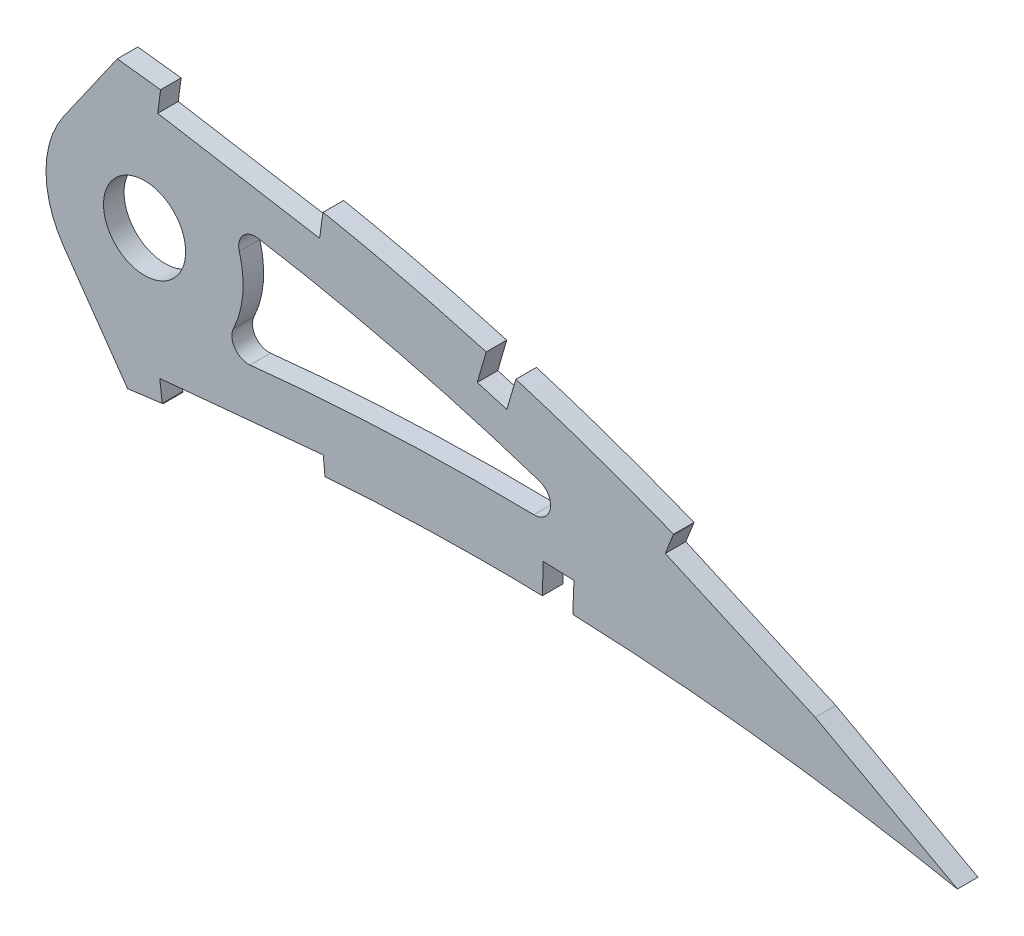
SolidWorks part; units mm, degrees
ref_plane "Front Plane" through (0, 0, 0) normal (0, 0, 1) x (1, 0, 0)
ref_plane "Top Plane" through (0, 0, 0) normal (0, 1, 0) x (1, 0, 0)
ref_plane "Right Plane" through (0, 0, 0) normal (1, 0, 0) x (0, 0, -1)
curve "Curve1"
  spline degree 3 poles (418.0125, 0.6517, 0) (417.9804, 0.6715, 0) (417.8525, 0.7505, 0) (417.5642, 0.9274, 0) (417.084, 1.2219, 0) (416.4119, 1.6322, 0) (415.5483, 2.157, 0) (414.4927, 2.7927, 0) (413.2459, 3.5372, 0) (411.8081, 4.387, 0) (410.1795, 5.3382, 0) (408.3608, 6.3869, 0) (406.352, 7.527, 0) (404.1539, 8.7541, 0) (401.7673, 10.0622, 0) (399.1927, 11.4455, 0) (396.4309, 12.8968, 0) (393.4831, 14.4101, 0) (390.3497, 15.9768, 0) (387.0323, 17.5905, 0) (383.532, 19.2431, 0) (379.8498, 20.9259, 0) (375.9881, 22.6319, 0) (371.9478, 24.3506, 0) (367.7312, 26.0745, 0) (363.3401, 27.7938, 0) (358.7771, 29.5006, 0) (354.0441, 31.184, 0) (349.1444, 32.8365, 0) (344.0806, 34.4474, 0) (338.8562, 36.008, 0) (333.4742, 37.5082, 0) (327.9392, 38.9402, 0) (322.2547, 40.2936, 0) (316.4254, 41.5594, 0) (310.456, 42.7299, 0) (304.3515, 43.7936, 0) (298.1289, 44.7494, 0) (291.8882, 45.5445, 0) (285.6603, 46.3243, 0) (279.4418, 47.0569, 0) (273.1472, 47.7584, 0) (266.7827, 48.425, 0) (260.3545, 49.0544, 0) (253.8692, 49.6441, 0) (247.3335, 50.1923, 0) (240.7538, 50.6959, 0) (234.1369, 51.1541, 0) (227.4895, 51.5628, 0) (220.8185, 51.9218, 0) (214.1308, 52.2286, 0) (207.4334, 52.481, 0) (200.7332, 52.6776, 0) (194.0374, 52.8164, 0) (187.3531, 52.8966, 0) (180.6873, 52.916, 0) (174.0473, 52.8742, 0) (167.44, 52.7698, 0) (160.8726, 52.6014, 0) (154.3521, 52.3686, 0) (147.8856, 52.0716, 0) (141.4801, 51.7078, 0) (135.1426, 51.2797, 0) (128.8802, 50.7853, 0) (122.6997, 50.2246, 0) (116.6076, 49.5999, 0) (110.6107, 48.9095, 0) (104.7154, 48.1553, 0) (98.9282, 47.3389, 0) (93.2555, 46.4598, 0) (87.7035, 45.5205, 0) (82.2781, 44.522, 0) (76.9851, 43.4673, 0) (71.8302, 42.3565, 0) (66.8189, 41.1931, 0) (61.9564, 39.979, 0) (57.2479, 38.7165, 0) (52.6982, 37.4086, 0) (48.3119, 36.0583, 0) (44.0941, 34.667, 0) (40.048, 33.2401, 0) (36.1786, 31.7785, 0) (32.4888, 30.2868, 0) (28.983, 28.767, 0) (25.6637, 27.2237, 0) (22.5348, 25.6586, 0) (19.5984, 24.0762, 0) (16.8576, 22.4789, 0) (14.3149, 20.8697, 0) (11.9714, 19.2526, 0) (9.8303, 17.6287, 0) (7.8925, 16.002, 0) (6.159, 14.375, 0) (4.6325, 12.7489, 0) (3.3127, 11.1265, 0) (2.2016, 9.5091, 0) (1.2991, 7.8983, 0) (0.6075, 6.2951, 0) (0.126, 4.7006, 0) (-0.1376, 3.117, 0) (-0.2032, 1.5431, 0) (-0.0676, 0.5136, 0) (0, 0, 0) knots 0 0 0 0 0.000254 0.001015 0.002283 0.004057 0.006331 0.009105 0.012374 0.016134 0.02038 0.025106 0.030306 0.035972 0.0421 0.048678 0.055702 0.06316 0.071046 0.07935 0.088063 0.097176 0.106678 0.116562 0.126814 0.137428 0.148394 0.1597 0.171338 0.183298 0.19557 0.208144 0.221012 0.234162 0.247587 0.261277 0.275223 0.289414 0.303771 0.317689 0.331784 0.34604 0.360444 0.374983 0.38964 0.404403 0.419257 0.434187 0.449177 0.464215 0.479284 0.49437 0.509458 0.524532 0.539579 0.554583 0.56953 0.584403 0.599191 0.613877 0.628447 0.642889 0.657186 0.671326 0.685294 0.699078 0.712665 0.726043 0.739198 0.752118 0.764792 0.777208 0.789356 0.801224 0.812804 0.824083 0.835055 0.84571 0.856038 0.866034 0.875689 0.884998 0.893953 0.902553 0.910789 0.918661 0.926166 0.933303 0.940071 0.946475 0.952518 0.958205 0.963547 0.968557 0.97325 0.977651 0.981787 0.985694 0.989415 0.993001 0.996508 1 1 1 1
curve "Curve2"
  spline degree 3 poles (0, 0, 0) (0.1073, -0.5067, 0) (0.3225, -1.5225, 0) (0.9071, -2.9849, 0) (1.6803, -4.3906, 0) (2.6581, -5.736, 0) (3.8343, -7.0207, 0) (5.206, -8.246, 0) (6.772, -9.4112, 0) (8.5303, -10.5159, 0) (10.4783, -11.5612, 0) (12.6138, -12.5465, 0) (14.9348, -13.4715, 0) (17.4389, -14.3348, 0) (20.1229, -15.1379, 0) (22.9843, -15.8787, 0) (26.0199, -16.5584, 0) (29.2267, -17.1751, 0) (32.6013, -17.7296, 0) (36.1401, -18.2214, 0) (39.8395, -18.651, 0) (43.6959, -19.0173, 0) (47.7054, -19.3212, 0) (51.8641, -19.5629, 0) (56.168, -19.7432, 0) (60.6128, -19.8613, 0) (65.1943, -19.9191, 0) (69.9083, -19.9175, 0) (74.7502, -19.8561, 0) (79.7159, -19.7382, 0) (84.8006, -19.5631, 0) (89.9997, -19.3329, 0) (95.3085, -19.05, 0) (100.7222, -18.7153, 0) (106.2362, -18.3302, 0) (111.8455, -17.8979, 0) (117.5452, -17.4195, 0) (123.3302, -16.8976, 0) (129.1955, -16.3351, 0) (135.1358, -15.7335, 0) (141.1461, -15.0958, 0) (147.221, -14.4241, 0) (153.3552, -13.7218, 0) (159.5432, -12.9903, 0) (165.7798, -12.2338, 0) (172.059, -11.4536, 0) (178.3757, -10.6529, 0) (184.7241, -9.8353, 0) (191.0984, -9.0009, 0) (197.493, -8.1554, 0) (203.902, -7.2983, 0) (210.3197, -6.4339, 0) (216.7401, -5.5649, 0) (223.157, -4.6917, 0) (229.5648, -3.8177, 0) (235.9575, -2.9455, 0) (242.3289, -2.075, 0) (248.6732, -1.2107, 0) (254.984, -0.3523, 0) (261.2554, 0.4983, 0) (267.4816, 1.3385, 0) (273.6565, 2.1675, 0) (279.7739, 2.9846, 0) (285.8276, 3.7901, 0) (291.7208, 4.5595, 0) (297.4382, 5.334, 0) (302.999, 5.9689, 0) (308.4906, 6.5107, 0) (313.9186, 6.955, 0) (319.2766, 7.3081, 0) (324.5584, 7.5724, 0) (329.7577, 7.7517, 0) (334.868, 7.8514, 0) (339.8828, 7.8739, 0) (344.7953, 7.8264, 0) (349.5992, 7.7127, 0) (354.2877, 7.538, 0) (358.8543, 7.3082, 0) (363.2925, 7.0294, 0) (367.5956, 6.7058, 0) (371.7576, 6.345, 0) (375.7722, 5.9523, 0) (379.6331, 5.5321, 0) (383.3347, 5.0933, 0) (386.8711, 4.6386, 0) (390.237, 4.1757, 0) (393.427, 3.7092, 0) (396.4359, 3.245, 0) (399.2592, 2.7876, 0) (401.8921, 2.3431, 0) (404.3306, 1.9155, 0) (406.5705, 1.5092, 0) (408.6087, 1.1291, 0) (410.4411, 0.7773, 0) (412.0652, 0.4594, 0) (413.4782, 0.1769, 0) (414.6777, -0.0662, 0) (415.6619, -0.269, 0) (416.4292, -0.4281, 0) (416.9781, -0.5438, 0) (417.3079, -0.6126, 0) (417.4545, -0.6439, 0) (417.4911, -0.6517, 0) knots 0 0 0 0 0.003638 0.007293 0.011028 0.014901 0.018963 0.023258 0.027821 0.032679 0.037853 0.043362 0.049215 0.055422 0.061989 0.068918 0.076211 0.083868 0.091887 0.100266 0.109 0.118085 0.127515 0.137285 0.147388 0.157816 0.168563 0.179619 0.190977 0.202627 0.21456 0.226767 0.239236 0.251959 0.264924 0.27812 0.291536 0.30516 0.318981 0.332985 0.347163 0.361499 0.375981 0.390597 0.405333 0.420175 0.43511 0.450124 0.465203 0.480333 0.495501 0.51069 0.525887 0.541078 0.556247 0.571382 0.586466 0.601485 0.616424 0.631269 0.646007 0.660621 0.675098 0.689423 0.703582 0.716908 0.730009 0.742952 0.755726 0.76832 0.780724 0.792927 0.804916 0.816679 0.828204 0.839475 0.850481 0.861208 0.871639 0.881763 0.891564 0.901027 0.910139 0.918884 0.927249 0.935221 0.942785 0.949928 0.956638 0.962904 0.968712 0.974054 0.978918 0.983297 0.98718 0.990561 0.993433 0.995791 0.99763 0.998946 0.999737 1 1 1 1
sketch "Sketch1" plane through (0, 0, 0) normal (0, 0, 1) x (1, 0, 0)
  line L25 (417.4911, -0.6517) -> (421.451, -1.4725)
  line L26 (418.0125, 0.6517) -> (421.451, -1.4725)
  spline S2 degree 3 poles (-2901.6072, -758.8258) (62.2286, 60.9377) (-7.5382, 18.1399) (0.9071, -2.9849) (1.6803, -4.3906) (2.6581, -5.736) (3.8343, -7.0207) (5.206, -8.246) (6.772, -9.4112) (8.5303, -10.5159) (10.4783, -11.5612) (12.6138, -12.5465) (14.9348, -13.4715) (17.4389, -14.3348) (20.1229, -15.1379) (22.9843, -15.8787) (26.0199, -16.5584) (29.2267, -17.1751) (32.6013, -17.7296) (36.1401, -18.2214) (39.8395, -18.651) (43.6959, -19.0173) (47.7054, -19.3212) (51.8641, -19.5629) (56.168, -19.7432) (60.6128, -19.8613) (65.1943, -19.9191) (69.9083, -19.9175) (74.7502, -19.8561) (79.7159, -19.7382) (84.8006, -19.5631) (89.9997, -19.3329) (95.3085, -19.05) (100.7222, -18.7153) (106.2362, -18.3302) (111.8455, -17.8979) (117.5452, -17.4195) (123.3302, -16.8976) (129.1955, -16.3351) (135.1358, -15.7335) (141.1461, -15.0958) (147.221, -14.4241) (153.3552, -13.7218) (159.5432, -12.9903) (165.7798, -12.2338) (172.059, -11.4536) (178.3757, -10.6529) (184.7241, -9.8353) (191.0984, -9.0009) (197.493, -8.1554) (203.902, -7.2983) (210.3197, -6.4339) (216.7401, -5.5649) (223.157, -4.6917) (229.5648, -3.8177) (235.9575, -2.9455) (242.3289, -2.075) (248.6732, -1.2107) (254.984, -0.3523) (261.2554, 0.4983) (267.4816, 1.3385) (273.6565, 2.1675) (279.7739, 2.9846) (285.8276, 3.7901) (291.7208, 4.5595) (297.4382, 5.334) (302.999, 5.9689) (308.4906, 6.5107) (313.9186, 6.955) (319.2766, 7.3081) (324.5584, 7.5724) (329.7577, 7.7517) (334.868, 7.8514) (339.8828, 7.8739) (344.7953, 7.8264) (349.5992, 7.7127) (354.2877, 7.538) (358.8543, 7.3082) (363.2925, 7.0294) (367.5956, 6.7058) (371.7576, 6.345) (375.7722, 5.9523) (379.6331, 5.5321) (383.3347, 5.0933) (386.8711, 4.6386) (390.237, 4.1757) (393.427, 3.7092) (396.4359, 3.245) (399.2592, 2.7876) (401.8921, 2.3431) (404.3306, 1.9155) (406.5705, 1.5092) (408.6087, 1.1291) (410.4411, 0.7773) (412.0652, 0.4594) (413.4782, 0.1769) (414.6777, -0.0662) (415.6619, -0.269) (416.4292, -0.4281) (416.9781, -0.5438) (432.6216, -3.8089) (446.5682, -14.1933) (1083.8628, 2923.4074) knots -0.148283 -0.148283 -0.148283 -0.148283 0.003638 0.007293 0.011028 0.014901 0.018963 0.023258 0.027821 0.032679 0.037853 0.043362 0.049215 0.055422 0.061989 0.068918 0.076211 0.083868 0.091887 0.100266 0.109 0.118085 0.127515 0.137285 0.147388 0.157816 0.168563 0.179619 0.190977 0.202627 0.21456 0.226767 0.239236 0.251959 0.264924 0.27812 0.291536 0.30516 0.318981 0.332985 0.347163 0.361499 0.375981 0.390597 0.405333 0.420175 0.43511 0.450124 0.465203 0.480333 0.495501 0.51069 0.525887 0.541078 0.556247 0.571382 0.586466 0.601485 0.616424 0.631269 0.646007 0.660621 0.675098 0.689423 0.703582 0.716908 0.730009 0.742952 0.755726 0.76832 0.780724 0.792927 0.804916 0.816679 0.828204 0.839475 0.850481 0.861208 0.871639 0.881763 0.891564 0.901027 0.910139 0.918884 0.927249 0.935221 0.942785 0.949928 0.956638 0.962904 0.968712 0.974054 0.978918 0.983297 0.98718 0.990561 0.993433 0.995791 0.99763 0.998946 0.999737 1.110049 1.110049 1.110049 1.110049 only from (0, 0) to (417.4911, -0.6517) construction
  spline S3 degree 3 poles (2035.6651, 2526.3996) (444.3669, -23.2124) (432.7668, -8.3977) (417.5642, 0.9274) (417.084, 1.2219) (416.4119, 1.6322) (415.5483, 2.157) (414.4927, 2.7927) (413.2459, 3.5372) (411.8081, 4.387) (410.1795, 5.3382) (408.3608, 6.3869) (406.352, 7.527) (404.1539, 8.7541) (401.7673, 10.0622) (399.1927, 11.4455) (396.4309, 12.8968) (393.4831, 14.4101) (390.3497, 15.9768) (387.0323, 17.5905) (383.532, 19.2431) (379.8498, 20.9259) (375.9881, 22.6319) (371.9478, 24.3506) (367.7312, 26.0745) (363.3401, 27.7938) (358.7771, 29.5006) (354.0441, 31.184) (349.1444, 32.8365) (344.0806, 34.4474) (338.8562, 36.008) (333.4742, 37.5082) (327.9392, 38.9402) (322.2547, 40.2936) (316.4254, 41.5594) (310.456, 42.7299) (304.3515, 43.7936) (298.1289, 44.7494) (291.8882, 45.5445) (285.6603, 46.3243) (279.4418, 47.0569) (273.1472, 47.7584) (266.7827, 48.425) (260.3545, 49.0544) (253.8692, 49.6441) (247.3335, 50.1923) (240.7538, 50.6959) (234.1369, 51.1541) (227.4895, 51.5628) (220.8185, 51.9218) (214.1308, 52.2286) (207.4334, 52.481) (200.7332, 52.6776) (194.0374, 52.8164) (187.3531, 52.8966) (180.6873, 52.916) (174.0473, 52.8742) (167.44, 52.7698) (160.8726, 52.6014) (154.3521, 52.3686) (147.8856, 52.0716) (141.4801, 51.7078) (135.1426, 51.2797) (128.8802, 50.7853) (122.6997, 50.2246) (116.6076, 49.5999) (110.6107, 48.9095) (104.7154, 48.1553) (98.9282, 47.3389) (93.2555, 46.4598) (87.7035, 45.5205) (82.2781, 44.522) (76.9851, 43.4673) (71.8302, 42.3565) (66.8189, 41.1931) (61.9564, 39.979) (57.2479, 38.7165) (52.6982, 37.4086) (48.3119, 36.0583) (44.0941, 34.667) (40.048, 33.2401) (36.1786, 31.7785) (32.4888, 30.2868) (28.983, 28.767) (25.6637, 27.2237) (22.5348, 25.6586) (19.5984, 24.0762) (16.8576, 22.4789) (14.3149, 20.8697) (11.9714, 19.2526) (9.8303, 17.6287) (7.8925, 16.002) (6.159, 14.375) (4.6325, 12.7489) (3.3127, 11.1265) (2.2016, 9.5091) (1.2991, 7.8983) (0.6075, 6.2951) (0.126, 4.7006) (-0.1376, 3.117) (-1.0834, -19.5745) (79.1081, -36.6721) (-2988.5065, -249.641) knots -0.11811 -0.11811 -0.11811 -0.11811 0.000254 0.001015 0.002283 0.004057 0.006331 0.009105 0.012374 0.016134 0.02038 0.025106 0.030306 0.035972 0.0421 0.048678 0.055702 0.06316 0.071046 0.07935 0.088063 0.097176 0.106678 0.116562 0.126814 0.137428 0.148394 0.1597 0.171338 0.183298 0.19557 0.208144 0.221012 0.234162 0.247587 0.261277 0.275223 0.289414 0.303771 0.317689 0.331784 0.34604 0.360444 0.374983 0.38964 0.404403 0.419257 0.434187 0.449177 0.464215 0.479284 0.49437 0.509458 0.524532 0.539579 0.554583 0.56953 0.584403 0.599191 0.613877 0.628447 0.642889 0.657186 0.671326 0.685294 0.699078 0.712665 0.726043 0.739198 0.752118 0.764792 0.777208 0.789356 0.801224 0.812804 0.824083 0.835055 0.84571 0.856038 0.866034 0.875689 0.884998 0.893953 0.902553 0.910789 0.918661 0.926166 0.933303 0.940071 0.946475 0.952518 0.958205 0.963547 0.968557 0.97325 0.977651 0.981787 0.985694 0.989415 0.993001 0.996508 1.142022 1.142022 1.142022 1.142022 only from (418.0125, 0.6517) to (0, 0) construction
  spline S4 degree 3 poles (0, 0) (0.1073, -0.5067) (0.3225, -1.5225) (0.9071, -2.9849) (1.6803, -4.3906) (2.6581, -5.736) (3.8343, -7.0207) (5.206, -8.246) (6.772, -9.4112) (8.5303, -10.5159) (10.4783, -11.5612) (12.6138, -12.5465) (14.9348, -13.4715) (17.4389, -14.3348) (20.1229, -15.1379) (22.9843, -15.8787) (26.0199, -16.5584) (29.2267, -17.1751) (32.6013, -17.7296) (36.1401, -18.2214) (39.8395, -18.651) (43.6959, -19.0173) (47.7054, -19.3212) (51.8641, -19.5629) (56.168, -19.7432) (60.6128, -19.8613) (65.1943, -19.9191) (69.9083, -19.9175) (74.7502, -19.8561) (79.7159, -19.7382) (84.8006, -19.5631) (89.9997, -19.3329) (95.3085, -19.05) (100.7222, -18.7153) (106.2362, -18.3302) (111.8455, -17.8979) (117.5452, -17.4195) (123.3302, -16.8976) (129.1955, -16.3351) (135.1358, -15.7335) (141.1461, -15.0958) (147.221, -14.4241) (153.3552, -13.7218) (159.5432, -12.9903) (165.7798, -12.2338) (172.059, -11.4536) (178.3757, -10.6529) (184.7241, -9.8353) (191.0984, -9.0009) (197.493, -8.1554) (203.902, -7.2983) (210.3197, -6.4339) (216.7401, -5.5649) (223.157, -4.6917) (229.5648, -3.8177) (235.9575, -2.9455) (242.3289, -2.075) (248.6732, -1.2107) (254.984, -0.3523) (261.2554, 0.4983) (267.4816, 1.3385) (273.6565, 2.1675) (279.7739, 2.9846) (285.8276, 3.7901) (291.7208, 4.5595) (297.4382, 5.334) (302.999, 5.9689) (308.4906, 6.5107) (313.9186, 6.955) (319.2766, 7.3081) (324.5584, 7.5724) (329.7577, 7.7517) (334.868, 7.8514) (339.8828, 7.8739) (344.7953, 7.8264) (349.5992, 7.7127) (354.2877, 7.538) (358.8543, 7.3082) (363.2925, 7.0294) (367.5956, 6.7058) (371.7576, 6.345) (375.7722, 5.9523) (379.6331, 5.5321) (383.3347, 5.0933) (386.8711, 4.6386) (390.237, 4.1757) (393.427, 3.7092) (396.4359, 3.245) (399.2592, 2.7876) (401.8921, 2.3431) (404.3306, 1.9155) (406.5705, 1.5092) (408.6087, 1.1291) (410.4411, 0.7773) (412.0652, 0.4594) (413.4782, 0.1769) (414.6777, -0.0662) (415.6619, -0.269) (416.4292, -0.4281) (416.9781, -0.5438) (417.3079, -0.6126) (417.4545, -0.6439) (417.4911, -0.6517) knots 0 0 0 0 0.003638 0.007293 0.011028 0.014901 0.018963 0.023258 0.027821 0.032679 0.037853 0.043362 0.049215 0.055422 0.061989 0.068918 0.076211 0.083868 0.091887 0.100266 0.109 0.118085 0.127515 0.137285 0.147388 0.157816 0.168563 0.179619 0.190977 0.202627 0.21456 0.226767 0.239236 0.251959 0.264924 0.27812 0.291536 0.30516 0.318981 0.332985 0.347163 0.361499 0.375981 0.390597 0.405333 0.420175 0.43511 0.450124 0.465203 0.480333 0.495501 0.51069 0.525887 0.541078 0.556247 0.571382 0.586466 0.601485 0.616424 0.631269 0.646007 0.660621 0.675098 0.689423 0.703582 0.716908 0.730009 0.742952 0.755726 0.76832 0.780724 0.792927 0.804916 0.816679 0.828204 0.839475 0.850481 0.861208 0.871639 0.881763 0.891564 0.901027 0.910139 0.918884 0.927249 0.935221 0.942785 0.949928 0.956638 0.962904 0.968712 0.974054 0.978918 0.983297 0.98718 0.990561 0.993433 0.995791 0.99763 0.998946 0.999737 1 1 1 1
  spline S5 degree 3 poles (418.0125, 0.6517) (417.9804, 0.6715) (417.8525, 0.7505) (417.5642, 0.9274) (417.084, 1.2219) (416.4119, 1.6322) (415.5483, 2.157) (414.4927, 2.7927) (413.2459, 3.5372) (411.8081, 4.387) (410.1795, 5.3382) (408.3608, 6.3869) (406.352, 7.527) (404.1539, 8.7541) (401.7673, 10.0622) (399.1927, 11.4455) (396.4309, 12.8968) (393.4831, 14.4101) (390.3497, 15.9768) (387.0323, 17.5905) (383.532, 19.2431) (379.8498, 20.9259) (375.9881, 22.6319) (371.9478, 24.3506) (367.7312, 26.0745) (363.3401, 27.7938) (358.7771, 29.5006) (354.0441, 31.184) (349.1444, 32.8365) (344.0806, 34.4474) (338.8562, 36.008) (333.4742, 37.5082) (327.9392, 38.9402) (322.2547, 40.2936) (316.4254, 41.5594) (310.456, 42.7299) (304.3515, 43.7936) (298.1289, 44.7494) (291.8882, 45.5445) (285.6603, 46.3243) (279.4418, 47.0569) (273.1472, 47.7584) (266.7827, 48.425) (260.3545, 49.0544) (253.8692, 49.6441) (247.3335, 50.1923) (240.7538, 50.6959) (234.1369, 51.1541) (227.4895, 51.5628) (220.8185, 51.9218) (214.1308, 52.2286) (207.4334, 52.481) (200.7332, 52.6776) (194.0374, 52.8164) (187.3531, 52.8966) (180.6873, 52.916) (174.0473, 52.8742) (167.44, 52.7698) (160.8726, 52.6014) (154.3521, 52.3686) (147.8856, 52.0716) (141.4801, 51.7078) (135.1426, 51.2797) (128.8802, 50.7853) (122.6997, 50.2246) (116.6076, 49.5999) (110.6107, 48.9095) (104.7154, 48.1553) (98.9282, 47.3389) (93.2555, 46.4598) (87.7035, 45.5205) (82.2781, 44.522) (76.9851, 43.4673) (71.8302, 42.3565) (66.8189, 41.1931) (61.9564, 39.979) (57.2479, 38.7165) (52.6982, 37.4086) (48.3119, 36.0583) (44.0941, 34.667) (40.048, 33.2401) (36.1786, 31.7785) (32.4888, 30.2868) (28.983, 28.767) (25.6637, 27.2237) (22.5348, 25.6586) (19.5984, 24.0762) (16.8576, 22.4789) (14.3149, 20.8697) (11.9714, 19.2526) (9.8303, 17.6287) (7.8925, 16.002) (6.159, 14.375) (4.6325, 12.7489) (3.3127, 11.1265) (2.2016, 9.5091) (1.2991, 7.8983) (0.6075, 6.2951) (0.126, 4.7006) (-0.1376, 3.117) (-0.2032, 1.5431) (-0.0676, 0.5136) (0, 0) knots 0 0 0 0 0.000254 0.001015 0.002283 0.004057 0.006331 0.009105 0.012374 0.016134 0.02038 0.025106 0.030306 0.035972 0.0421 0.048678 0.055702 0.06316 0.071046 0.07935 0.088063 0.097176 0.106678 0.116562 0.126814 0.137428 0.148394 0.1597 0.171338 0.183298 0.19557 0.208144 0.221012 0.234162 0.247587 0.261277 0.275223 0.289414 0.303771 0.317689 0.331784 0.34604 0.360444 0.374983 0.38964 0.404403 0.419257 0.434187 0.449177 0.464215 0.479284 0.49437 0.509458 0.524532 0.539579 0.554583 0.56953 0.584403 0.599191 0.613877 0.628447 0.642889 0.657186 0.671326 0.685294 0.699078 0.712665 0.726043 0.739198 0.752118 0.764792 0.777208 0.789356 0.801224 0.812804 0.824083 0.835055 0.84571 0.856038 0.866034 0.875689 0.884998 0.893953 0.902553 0.910789 0.918661 0.926166 0.933303 0.940071 0.946475 0.952518 0.958205 0.963547 0.968557 0.97325 0.977651 0.981787 0.985694 0.989415 0.993001 0.996508 1 1 1 1
extrude "Boss-Extrude1" add sketch "Sketch1" along normal blind 3.175
sketch "Sketch3" plane through (0, 0, 0) normal (0, 0, -1) x (-1, 0, 0)
  circle A1 centre (-285.7292, 26.2554) radius 6.35
extrude "Cut-Extrude2" cut sketch "Sketch3" against normal blind 7.62
sketch "Sketch4" plane through (0, 0, 3.175) normal (0, 0, 1) x (1, 0, 0)
  line L0 (273.2453, 34.9967) -> (281.5171, 46.8101)
  line L1 (273.2453, 17.5141) -> (283.1086, 3.4278)
  line L2 (285.7292, 26.2554) -> (311.044, 26.2554)
  circle A0 centre (285.7292, 26.2554) radius 6.35 construction
  circle A1 centre (285.7292, 26.2554) radius 6.35
  circle A2 centre (285.7292, 26.2554) radius 15.24
  spline S0 degree 3 poles (-1937.7253, -493.2296) (46.5589, 50.9528) (-6.5452, 15.6559) (0.9071, -2.9849) (1.6803, -4.3906) (2.6581, -5.736) (3.8343, -7.0207) (5.206, -8.246) (6.772, -9.4112) (8.5303, -10.5159) (10.4783, -11.5612) (12.6138, -12.5465) (14.9348, -13.4715) (17.4389, -14.3348) (20.1229, -15.1379) (22.9843, -15.8787) (26.0199, -16.5584) (29.2267, -17.1751) (32.6013, -17.7296) (36.1401, -18.2214) (39.8395, -18.651) (43.6959, -19.0173) (47.7054, -19.3212) (51.8641, -19.5629) (56.168, -19.7432) (60.6128, -19.8613) (65.1943, -19.9191) (69.9083, -19.9175) (74.7502, -19.8561) (79.7159, -19.7382) (84.8006, -19.5631) (89.9997, -19.3329) (95.3085, -19.05) (100.7222, -18.7153) (106.2362, -18.3302) (111.8455, -17.8979) (117.5452, -17.4195) (123.3302, -16.8976) (129.1955, -16.3351) (135.1358, -15.7335) (141.1461, -15.0958) (147.221, -14.4241) (153.3552, -13.7218) (159.5432, -12.9903) (165.7798, -12.2338) (172.059, -11.4536) (178.3757, -10.6529) (184.7241, -9.8353) (191.0984, -9.0009) (197.493, -8.1554) (203.902, -7.2983) (210.3197, -6.4339) (216.7401, -5.5649) (223.157, -4.6917) (229.5648, -3.8177) (235.9575, -2.9455) (242.3289, -2.075) (248.6732, -1.2107) (254.984, -0.3523) (261.2554, 0.4983) (267.4816, 1.3385) (273.6565, 2.1675) (279.7739, 2.9846) (285.8276, 3.7901) (291.7208, 4.5595) (297.4382, 5.334) (302.999, 5.9689) (308.4906, 6.5107) (313.9186, 6.955) (319.2766, 7.3081) (324.5584, 7.5724) (329.7577, 7.7517) (334.868, 7.8514) (339.8828, 7.8739) (344.7953, 7.8264) (349.5992, 7.7127) (354.2877, 7.538) (358.8543, 7.3082) (363.2925, 7.0294) (367.5956, 6.7058) (371.7576, 6.345) (375.7722, 5.9523) (379.6331, 5.5321) (383.3347, 5.0933) (386.8711, 4.6386) (390.237, 4.1757) (393.427, 3.7092) (396.4359, 3.245) (399.2592, 2.7876) (401.8921, 2.3431) (404.3306, 1.9155) (406.5705, 1.5092) (408.6087, 1.1291) (410.4411, 0.7773) (412.0652, 0.4594) (413.4782, 0.1769) (414.6777, -0.0662) (415.6619, -0.269) (416.4292, -0.4281) (416.9781, -0.5438) (430.6853, -3.4047) (443.0511, -11.7044) (871.2046, 1946.5522) knots -0.129551 -0.129551 -0.129551 -0.129551 0.003638 0.007293 0.011028 0.014901 0.018963 0.023258 0.027821 0.032679 0.037853 0.043362 0.049215 0.055422 0.061989 0.068918 0.076211 0.083868 0.091887 0.100266 0.109 0.118085 0.127515 0.137285 0.147388 0.157816 0.168563 0.179619 0.190977 0.202627 0.21456 0.226767 0.239236 0.251959 0.264924 0.27812 0.291536 0.30516 0.318981 0.332985 0.347163 0.361499 0.375981 0.390597 0.405333 0.420175 0.43511 0.450124 0.465203 0.480333 0.495501 0.51069 0.525887 0.541078 0.556247 0.571382 0.586466 0.601485 0.616424 0.631269 0.646007 0.660621 0.675098 0.689423 0.703582 0.716908 0.730009 0.742952 0.755726 0.76832 0.780724 0.792927 0.804916 0.816679 0.828204 0.839475 0.850481 0.861208 0.871639 0.881763 0.891564 0.901027 0.910139 0.918884 0.927249 0.935221 0.942785 0.949928 0.956638 0.962904 0.968712 0.974054 0.978918 0.983297 0.98718 0.990561 0.993433 0.995791 0.99763 0.998946 0.999737 1.096134 1.096134 1.096134 1.096134 only from (0, 0) to (417.4911, -0.6517) construction
  spline S1 degree 3 poles (1505.5404, 1678.541) (441.4039, -19.5852) (430.8807, -7.2408) (417.5642, 0.9274) (417.084, 1.2219) (416.4119, 1.6322) (415.5483, 2.157) (414.4927, 2.7927) (413.2459, 3.5372) (411.8081, 4.387) (410.1795, 5.3382) (408.3608, 6.3869) (406.352, 7.527) (404.1539, 8.7541) (401.7673, 10.0622) (399.1927, 11.4455) (396.4309, 12.8968) (393.4831, 14.4101) (390.3497, 15.9768) (387.0323, 17.5905) (383.532, 19.2431) (379.8498, 20.9259) (375.9881, 22.6319) (371.9478, 24.3506) (367.7312, 26.0745) (363.3401, 27.7938) (358.7771, 29.5006) (354.0441, 31.184) (349.1444, 32.8365) (344.0806, 34.4474) (338.8562, 36.008) (333.4742, 37.5082) (327.9392, 38.9402) (322.2547, 40.2936) (316.4254, 41.5594) (310.456, 42.7299) (304.3515, 43.7936) (298.1289, 44.7494) (291.8882, 45.5445) (285.6603, 46.3243) (279.4418, 47.0569) (273.1472, 47.7584) (266.7827, 48.425) (260.3545, 49.0544) (253.8692, 49.6441) (247.3335, 50.1923) (240.7538, 50.6959) (234.1369, 51.1541) (227.4895, 51.5628) (220.8185, 51.9218) (214.1308, 52.2286) (207.4334, 52.481) (200.7332, 52.6776) (194.0374, 52.8164) (187.3531, 52.8966) (180.6873, 52.916) (174.0473, 52.8742) (167.44, 52.7698) (160.8726, 52.6014) (154.3521, 52.3686) (147.8856, 52.0716) (141.4801, 51.7078) (135.1426, 51.2797) (128.8802, 50.7853) (122.6997, 50.2246) (116.6076, 49.5999) (110.6107, 48.9095) (104.7154, 48.1553) (98.9282, 47.3389) (93.2555, 46.4598) (87.7035, 45.5205) (82.2781, 44.522) (76.9851, 43.4673) (71.8302, 42.3565) (66.8189, 41.1931) (61.9564, 39.979) (57.2479, 38.7165) (52.6982, 37.4086) (48.3119, 36.0583) (44.0941, 34.667) (40.048, 33.2401) (36.1786, 31.7785) (32.4888, 30.2868) (28.983, 28.767) (25.6637, 27.2237) (22.5348, 25.6586) (19.5984, 24.0762) (16.8576, 22.4789) (14.3149, 20.8697) (11.9714, 19.2526) (9.8303, 17.6287) (7.8925, 16.002) (6.159, 14.375) (4.6325, 12.7489) (3.3127, 11.1265) (2.2016, 9.5091) (1.2991, 7.8983) (0.6075, 6.2951) (0.126, 4.7006) (-0.1376, 3.117) (-0.9722, -16.9072) (60.9773, -32.4825) (-1991.3982, -179.4503) knots -0.103174 -0.103174 -0.103174 -0.103174 0.000254 0.001015 0.002283 0.004057 0.006331 0.009105 0.012374 0.016134 0.02038 0.025106 0.030306 0.035972 0.0421 0.048678 0.055702 0.06316 0.071046 0.07935 0.088063 0.097176 0.106678 0.116562 0.126814 0.137428 0.148394 0.1597 0.171338 0.183298 0.19557 0.208144 0.221012 0.234162 0.247587 0.261277 0.275223 0.289414 0.303771 0.317689 0.331784 0.34604 0.360444 0.374983 0.38964 0.404403 0.419257 0.434187 0.449177 0.464215 0.479284 0.49437 0.509458 0.524532 0.539579 0.554583 0.56953 0.584403 0.599191 0.613877 0.628447 0.642889 0.657186 0.671326 0.685294 0.699078 0.712665 0.726043 0.739198 0.752118 0.764792 0.777208 0.789356 0.801224 0.812804 0.824083 0.835055 0.84571 0.856038 0.866034 0.875689 0.884998 0.893953 0.902553 0.910789 0.918661 0.926166 0.933303 0.940071 0.946475 0.952518 0.958205 0.963547 0.968557 0.97325 0.977651 0.981787 0.985694 0.989415 0.993001 0.996508 1.124083 1.124083 1.124083 1.124083 only from (418.0125, 0.6517) to (0, 0) construction
  spline S2 degree 3 poles (180.4181, -10.3891) (181.8505, -10.2052) (185.4085, -9.7457) (191.0984, -9.0009) (197.493, -8.1554) (203.902, -7.2983) (210.3197, -6.4339) (216.7401, -5.5649) (223.157, -4.6917) (229.5648, -3.8177) (235.9575, -2.9455) (242.3289, -2.075) (248.6732, -1.2107) (254.984, -0.3523) (261.2554, 0.4983) (267.4816, 1.3385) (273.6565, 2.1675) (279.7739, 2.9846) (285.8276, 3.7901) (291.7208, 4.5595) (297.4382, 5.334) (302.999, 5.9689) (308.4906, 6.5107) (313.9186, 6.955) (319.2766, 7.3081) (324.5584, 7.5724) (329.7577, 7.7517) (334.868, 7.8514) (339.8828, 7.8739) (344.7953, 7.8264) (349.5992, 7.7127) (354.2877, 7.538) (358.8543, 7.3082) (363.2925, 7.0294) (367.5956, 6.7058) (371.7576, 6.345) (375.7722, 5.9523) (379.6331, 5.5321) (383.3347, 5.0933) (386.8711, 4.6386) (390.237, 4.1757) (393.427, 3.7092) (396.4359, 3.245) (399.2592, 2.7876) (401.8921, 2.3431) (404.3306, 1.9155) (406.5705, 1.5092) (408.6087, 1.1291) (410.4411, 0.7773) (412.0652, 0.4594) (413.4782, 0.1769) (414.6777, -0.0662) (415.6619, -0.269) (416.4292, -0.4281) (416.9781, -0.5438) (417.3079, -0.6126) (417.4545, -0.6439) (417.4911, -0.6517) knots 0.439965 0.439965 0.439965 0.439965 0.450124 0.465203 0.480333 0.495501 0.51069 0.525887 0.541078 0.556247 0.571382 0.586466 0.601485 0.616424 0.631269 0.646007 0.660621 0.675098 0.689423 0.703582 0.716908 0.730009 0.742952 0.755726 0.76832 0.780724 0.792927 0.804916 0.816679 0.828204 0.839475 0.850481 0.861208 0.871639 0.881763 0.891564 0.901027 0.910139 0.918884 0.927249 0.935221 0.942785 0.949928 0.956638 0.962904 0.968712 0.974054 0.978918 0.983297 0.98718 0.990561 0.993433 0.995791 0.99763 0.998946 0.999737 1 1 1 1
  spline S3 degree 3 poles (418.0125, 0.6517) (417.9804, 0.6715) (417.8525, 0.7505) (417.5642, 0.9274) (417.084, 1.2219) (416.4119, 1.6322) (415.5483, 2.157) (414.4927, 2.7927) (413.2459, 3.5372) (411.8081, 4.387) (410.1795, 5.3382) (408.3608, 6.3869) (406.352, 7.527) (404.1539, 8.7541) (401.7673, 10.0622) (399.1927, 11.4455) (396.4309, 12.8968) (393.4831, 14.4101) (390.3497, 15.9768) (387.0323, 17.5905) (383.532, 19.2431) (379.8498, 20.9259) (375.9881, 22.6319) (371.9478, 24.3506) (367.7312, 26.0745) (363.3401, 27.7938) (358.7771, 29.5006) (354.0441, 31.184) (349.1444, 32.8365) (344.0806, 34.4474) (338.8562, 36.008) (333.4742, 37.5082) (327.9392, 38.9402) (322.2547, 40.2936) (316.4254, 41.5594) (310.456, 42.7299) (304.3515, 43.7936) (298.1289, 44.7494) (291.8882, 45.5445) (285.6603, 46.3243) (279.4418, 47.0569) (273.1472, 47.7584) (266.7827, 48.425) (260.3545, 49.0544) (253.8692, 49.6441) (247.3335, 50.1923) (240.7538, 50.6959) (234.1369, 51.1541) (227.4895, 51.5628) (220.8185, 51.9218) (214.1308, 52.2286) (207.4334, 52.481) (200.7332, 52.6776) (194.0374, 52.8164) (187.3531, 52.8966) (180.6873, 52.916) (174.0473, 52.8742) (167.44, 52.7698) (160.8726, 52.6014) (155.4817, 52.4089) (152.281, 52.2704) (151.2539, 52.2234) knots 0 0 0 0 0.000254 0.001015 0.002283 0.004057 0.006331 0.009105 0.012374 0.016134 0.02038 0.025106 0.030306 0.035972 0.0421 0.048678 0.055702 0.06316 0.071046 0.07935 0.088063 0.097176 0.106678 0.116562 0.126814 0.137428 0.148394 0.1597 0.171338 0.183298 0.19557 0.208144 0.221012 0.234162 0.247587 0.261277 0.275223 0.289414 0.303771 0.317689 0.331784 0.34604 0.360444 0.374983 0.38964 0.404403 0.419257 0.434187 0.449177 0.464215 0.479284 0.49437 0.509458 0.524532 0.539579 0.554583 0.56953 0.584403 0.599191 0.613877 0.620817 0.620817 0.620817 0.620817
  spline S4 degree 1 poles (412.6728, -7.992) (151.7184, 42.0741) knots 0 0 1 1 construction
  spline S5 degree 3 poles (412.6728, -7.992) (412.529, -7.9032) (412.2464, -7.7298) (411.6377, -7.3565) (410.5993, -6.7234) (408.5143, -5.4652) (404.306, -2.9803) (395.8163, 1.8196) (378.4768, 10.7592) (357.9235, 19.3569) (336.7625, 26.1844) (323.3258, 29.6855) (312.4652, 32.0171) (305.6501, 33.2719) (300.1537, 34.1638) (296.076, 34.7616) (291.9086, 35.3008) (286.2081, 36.0188) (279.1798, 36.867) (267.8599, 38.1235) (253.7183, 39.5037) (236.7158, 40.8444) (214.0351, 42.1902) (185.6608, 43.0017) (163.0284, 42.5917) (151.7184, 42.0741) knots 0 0 0 0 0.001213 0.002425 0.00485 0.0097 0.019401 0.038801 0.077602 0.155204 0.194005 0.232807 0.252207 0.271608 0.281308 0.291008 0.300708 0.310409 0.329809 0.34921 0.388011 0.426812 0.465613 0.543215 0.620817 0.620817 0.620817 0.620817
  spline S6 degree 1 poles (179.1239, -0.3119) (419.6107, 9.2848) knots 0 0 1 1 construction
  spline S7 degree 3 poles (179.1239, -0.3119) (188.9725, 0.9529) (208.644, 3.5759) (233.2881, 6.9462) (253.0144, 9.6358) (267.829, 11.6393) (278.9188, 13.1245) (286.3557, 14.1051) (290.0348, 14.5872) (293.7202, 15.0843) (297.5682, 15.5751) (301.3934, 16.0072) (306.4806, 16.5301) (315.4288, 17.2991) (328.2209, 17.9712) (343.5941, 18.1039) (364.063, 17.4008) (384.4368, 15.4184) (402.073, 12.6709) (410.8627, 11.0539) (415.2186, 10.1932) (417.2602, 9.7755) (418.1832, 9.5844) (418.673, 9.4822) (419.1054, 9.3912) (419.4468, 9.3197) (419.6107, 9.2848) knots 0.439965 0.439965 0.439965 0.439965 0.50997 0.579974 0.614976 0.649978 0.684981 0.693731 0.702482 0.711232 0.719983 0.728733 0.737484 0.754985 0.789987 0.824989 0.859991 0.929996 0.964998 0.982499 0.991249 0.995625 0.996719 0.997812 0.998906 1 1 1 1
  dimension "D2" = 30.48
  dimension "D1" = 10.16
  dimension "D3" = 55
  dimension "D4" = 55
extrude "Cut-Extrude3" cut sketch "Sketch4" against normal through all
sketch "Sketch5" plane through (0, 0, 3.175) normal (0, 0, 1) x (1, 0, 0)
  line L0 (313.2274, 41.5607) -> (288.1734, 45.7764)
  line L1 (313.2274, 41.5607) -> (288.1734, 45.7764)
  line L2 (288.1734, 45.7764) -> (287.7598, 42.6289)
  line L3 (288.1734, 45.7764) -> (287.7598, 42.6289)
  line L4 (313.3548, 9.6884) -> (288.0769, 7.29)
  line L5 (313.3548, 9.6884) -> (288.0769, 7.29)
  line L6 (288.0769, 7.29) -> (288.4652, 4.1389)
  line L7 (288.0769, 7.29) -> (288.4652, 4.1389)
  line L8 (343.075, 34.5005) -> (338.4925, 35.8715)
  line L9 (343.075, 34.5005) -> (338.4925, 35.8715)
  line L10 (338.4925, 35.8715) -> (337.1636, 31.2987)
  line L11 (338.4925, 35.8715) -> (337.1636, 31.2987)
  line L12 (352.1156, 12.2562) -> (347.3577, 12.4472)
  line L13 (352.1156, 12.2562) -> (347.3577, 12.4472)
  line L14 (347.3577, 12.4472) -> (347.2307, 7.687)
  line L15 (347.3577, 12.4472) -> (347.2307, 7.687)
  line L16 (390.5966, 15.5315) -> (367.4044, 25.8811)
  line L17 (390.5966, 15.5315) -> (367.4044, 25.8811)
  line L18 (367.4044, 25.8811) -> (366.2309, 22.9317)
  line L19 (367.4044, 25.8811) -> (366.2309, 22.9317)
  line L20 (413.2407, 3.2048) -> (390.9437, 15.3691)
  line L21 (413.2407, 3.2048) -> (390.9437, 15.3691)
  line L22 (411.7201, 0.4177) -> (413.2407, 3.2048)
  line L23 (411.7201, 0.4177) -> (413.2407, 3.2048)
  line L24 (389.4231, 12.582) -> (411.7201, 0.4177)
  line L25 (389.4231, 12.582) -> (411.7201, 0.4177)
  line L26 (366.2309, 22.9317) -> (389.4231, 12.582)
  line L27 (366.2309, 22.9317) -> (389.4231, 12.582)
  line L28 (341.7364, 29.9698) -> (343.075, 34.5005)
  line L29 (341.7364, 29.9698) -> (343.075, 34.5005)
  line L30 (337.1636, 31.2987) -> (341.7364, 29.9698)
  line L31 (337.1636, 31.2987) -> (341.7364, 29.9698)
  line L32 (351.9259, 7.5302) -> (352.1156, 12.2562)
  line L33 (351.9259, 7.5302) -> (352.1156, 12.2562)
  line L34 (347.2307, 7.687) -> (351.9259, 7.5302)
  line L35 (347.2307, 7.687) -> (351.9259, 7.5302)
  line L36 (312.7925, 38.4157) -> (313.2274, 41.5607)
  line L37 (312.7925, 38.4157) -> (313.2274, 41.5607)
  line L38 (287.7598, 42.6289) -> (312.7925, 38.4157)
  line L39 (287.7598, 42.6289) -> (312.7925, 38.4157)
  line L40 (313.6552, 6.5288) -> (313.3548, 9.6884)
  line L41 (313.6552, 6.5288) -> (313.3548, 9.6884)
  line L42 (288.4652, 4.1389) -> (313.6552, 6.5288)
  line L43 (288.4652, 4.1389) -> (313.6552, 6.5288)
  line L44 (288.1734, 45.7764) -> (288.632, 49.2661)
  line L45 (313.2274, 41.5607) -> (313.7484, 44.6574)
  line L46 (338.4925, 35.8715) -> (338.9628, 37.49)
  line L47 (343.075, 34.5005) -> (343.5374, 36.0657)
  line L48 (367.4044, 25.8811) -> (369.4696, 31.0537)
  line L49 (369.4696, 31.0537) -> (430.866, 31.0537)
  line L50 (430.866, 31.0537) -> (430.866, -10.0275)
  line L51 (430.866, -10.0275) -> (411.7201, 0.4177)
extrude "Cut-Extrude4" cut sketch "Sketch5" against normal through all
fillet "Fillet1" radius 2.54 3 edges at (362.3528, 17.2653, 1.5875) (296.4559, 15.4298, 1.5875) (298.6195, 34.3854, 1.5875)
